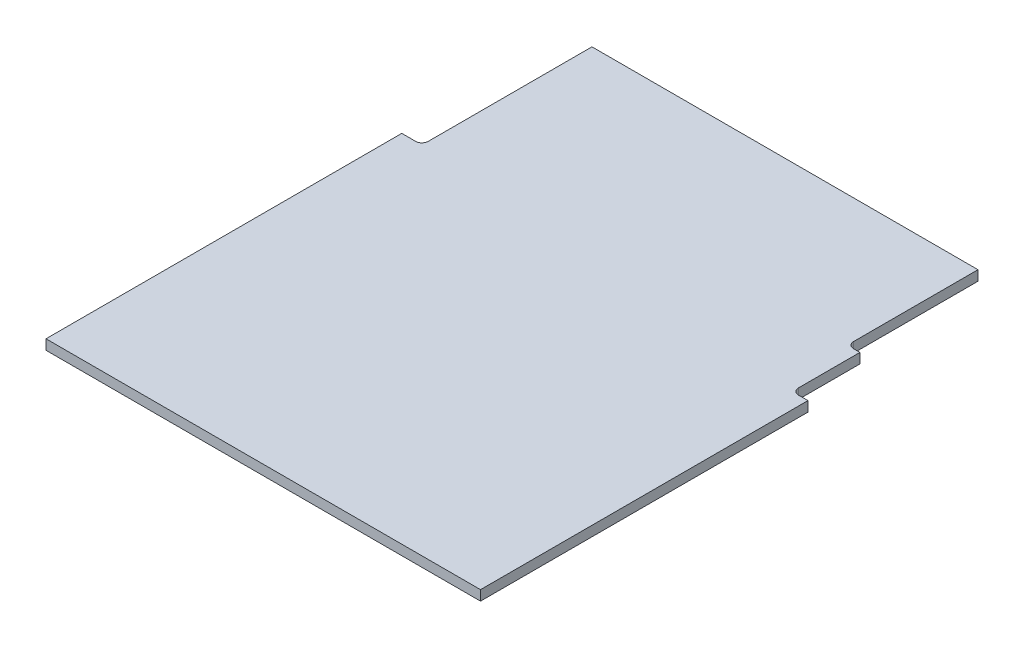
SolidWorks part; units mm, degrees
ref_plane "Front" through (0, 0, 0) normal (0, 0, 1) x (1, 0, 0)
ref_plane "Top" through (0, 0, 0) normal (0, 1, 0) x (1, 0, 0)
ref_plane "Right" through (0, 0, 0) normal (1, 0, 0) x (0, 0, -1)
sketch "Sketch1" plane through (0, 0, 0) normal (0, 1, 0) x (1, 0, 0)
  line L0 (-34.5, -9) -> (-34.5, -16) construction
  line L1 (-34.5, -9) -> (34.5, -9) construction
  line L2 (-34.5, -9) -> (-34.5, 67.5) construction
  line L3 (-34.5, 67.5) -> (34.5, 67.5) construction
  line L4 (34.5, -9) -> (34.5, 67.5) construction
  line L5 (-34.5, -16) -> (34.5, -16) construction
  line L6 (34.5, -16) -> (34.5, -9) construction
  line L7 (34.5, -9) -> (34.5, 36)
  line L8 (34.5, 36) -> (32, 36) construction
  line L9 (32, 36) -> (32, 46.75) construction
  line L10 (32, 46.75) -> (30, 46.75) construction
  line L11 (30, 46.75) -> (30, 67.5) construction
  line L12 (30, 67.5) -> (-31.3, 67.5)
  line L13 (-31.3, 67.5) -> (-31.3, 40.5) construction
  line L14 (-31.3, 40.5) -> (-34.5, 40.5) construction
  line L15 (-34.5, 40.5) -> (-34.5, -9)
  line L16 (30, 67.5) -> (30, 47.75)
  line L17 (31, 46.75) -> (32, 46.75)
  line L18 (32, 46.75) -> (32, 37)
  line L19 (32.94, 36) -> (34.5, 36)
  line L20 (-31.3, 67.5) -> (-31.3, 41.5)
  line L21 (-32.2185, 40.5) -> (-34.5, 40.5)
  line L22 (-34.5, -9) -> (-34.5, -16)
  line L23 (-34.5, -16) -> (34.5, -16)
  line L24 (34.5, -16) -> (34.5, -9)
  arc A0 (30, 47.75) -> (31, 46.75) centre (31, 47.75) ccw
  arc A1 (32, 37) -> (32.94, 36) centre (33.0019, 37) ccw
  arc A2 (-31.3, 41.5) -> (-32.2185, 40.5) centre (-32.3036, 41.5) cw
extrude "FR4" add sketch "Sketch1" along normal blind 1.5875
